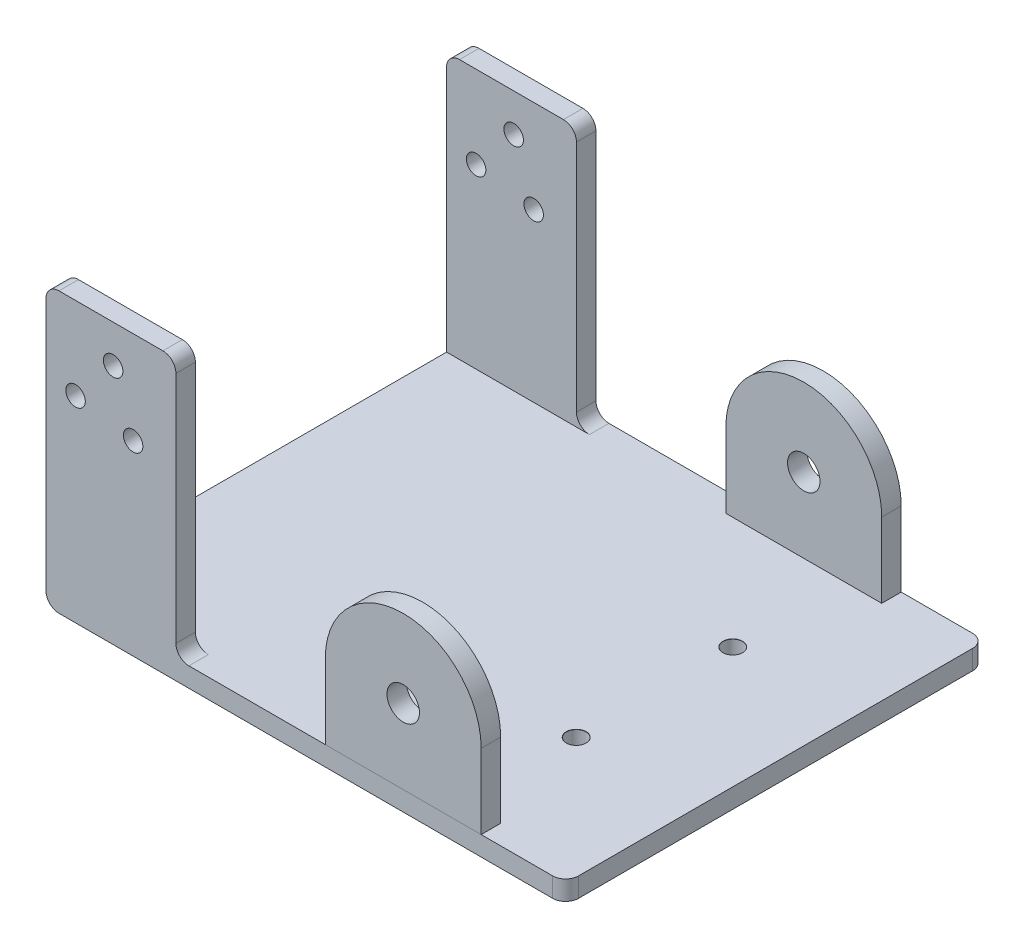
SolidWorks part; units mm, degrees
material "ABS"
ref_plane "Front Plane" through (0, 0, 0) normal (0, 0, 1) x (1, 0, 0)
ref_plane "Top Plane" through (0, 0, 0) normal (0, 1, 0) x (1, 0, 0)
ref_plane "Right Plane" through (0, 0, 0) normal (1, 0, 0) x (0, 0, -1)
sketch "Sketch1" plane through (0, 0, 0) normal (0, 1, 0) x (1, 0, 0)
  line L1 (-40, -32.335) -> (40, -32.335)
  line L2 (-40, -32.335) -> (-40, 32.335)
  line L3 (-40, 32.335) -> (40, 32.335)
  line L4 (40, -32.335) -> (40, 32.335)
  line L5 (-40, -32.335) -> (40, 32.335) construction
  line L6 (-40, 32.335) -> (40, -32.335) construction
  point P0 (0, 0)
  dimension "D1" = 80
  dimension "D2" = 64.67
extrude "Boss-Extrude1" add sketch "Sketch1" along normal blind 3
sketch "Sketch2" plane through (0, 3, 0) normal (0, 1, 0) x (1, 0, 0)
  line L1 (-40, 32.335) -> (-20, 32.335)
  line L2 (-40, 32.335) -> (-40, 29.335)
  line L3 (-40, 29.335) -> (-20, 29.335)
  line L4 (-20, 32.335) -> (-20, 29.335)
  line L5 (-40, -32.335) -> (-20, -32.335)
  line L6 (-40, -32.335) -> (-40, -29.335)
  line L7 (-40, -29.335) -> (-20, -29.335)
  line L8 (-20, -32.335) -> (-20, -29.335)
  dimension "D1" = 3
  dimension "D2" = 20
extrude "Boss-Extrude2" add sketch "Sketch2" along normal blind 40
hole_wizard "Ø3.0mm Dowel Hole1" positions "Sketch3" profile "Sketch4" hole size "Ø3.0" standard "ANSI Metric" end condition through all
sketch "Sketch3" plane through (0, 0, -32.335) normal (0, 0, -1) x (-1, 0, 0)
  point P0 (26.5872, 28.721)
  point P3 (35.4504, 30.2838)
  point P6 (29.6653, 37.1782)
sketch "Sketch4" plane through (-26.5872, 28.721, -32.335) normal (1, 0, 0) x (0, 1, 0)
  line L0 (0, 0) -> (0, 64.67)
  line L1 (0, 64.67) -> (1.5, 64.67)
  line L2 (1.5, 64.67) -> (1.5, 0.025)
  line L3 (1.5, 0.025) -> (1.525, 0)
  line L5 (1.525, 0) -> (0, 0)
  line L6 (-1.5, 0.025) -> (-1.525, 0) construction
  line L11 (0, -6.35) -> (0, 107.95) construction
  dimension "Thru Hole Dia." = 3
  dimension "Thru Hole Depth" = 64.67
  dimension "Near C'Sink Dia." = 3.05
  dimension "Near C'Sink Angle" = 90
fillet "Fillet1" radius 2 9 edges at (40, 1.5, -32.335) (40, 1.5, 32.335) (-40, 43, -30.835) (-20, 3, -30.835) (-20, 3, 30.835) (-20, 43, 30.835) (-40, 43, 30.835) (-20, 43, -30.835) (-40, 0, 0)
hole_wizard "Ø3.0mm Dowel Hole2" positions "Sketch7" profile "Sketch8" hole size "Ø3.0" standard "ANSI Metric" end condition through all
sketch "Sketch7" plane through (0, 3, 0) normal (0, 1, 0) x (1, 0, 0)
  point P0 (21.35, 12.05)
  point P3 (21.35, -12.05)
sketch "Sketch8" plane through (21.35, 3, -12.05) normal (1, 0, 0) x (0, 0, 1)
  line L0 (0, 0) -> (0, 3)
  line L1 (0, 3) -> (1.5, 3)
  line L2 (1.5, 3) -> (1.5, 0.025)
  line L3 (1.5, 0.025) -> (1.525, 0)
  line L5 (1.525, 0) -> (0, 0)
  line L6 (-1.5, 0.025) -> (-1.525, 0) construction
  line L11 (0, -6.35) -> (0, 107.95) construction
  dimension "Thru Hole Dia." = 3
  dimension "Thru Hole Depth" = 3
  dimension "Near C'Sink Dia." = 3.05
  dimension "Near C'Sink Angle" = 90
sketch "Sketch9" plane through (0, 0, -32.335) normal (0, 0, -1) x (-1, 0, 0)
  line L0 (-27, 3) -> (-27, 14.5)
  line L1 (-38, 3) -> (18, 3) construction
  line L2 (-27, 3) -> (-3, 3)
  line L3 (-3, 3) -> (-3, 14.5)
  line L4 (-40, 0) -> (-40, 3) construction
  line L5 (-38, 0) -> (38, 0) construction
  arc A0 (-27, 14.5) -> (-3, 14.5) centre (-15, 14.5) cw
  circle A1 centre (-15, 14.5) radius 2.5
  dimension "D3" = 12
  dimension "D4" = 5
  dimension "D1" = 25
  dimension "D2" = 14.5
extrude "Boss-Extrude3" add sketch "Sketch9" against normal blind 3 separate body
sketch "Sketch10" plane through (0, 0, 32.335) normal (0, 0, 1) x (1, 0, 0)
  line L0 (-18, 3) -> (38, 3) construction
  line L1 (3, 3) -> (27, 3)
  line L3 (3, 3) -> (27, 3)
  line L4 (27, 3) -> (27, 14.5)
  line L5 (3, 14.5) -> (3, 3)
  line L7 (27, 3) -> (27, 14.5)
  line L8 (3, 14.5) -> (3, 3)
  circle A0 centre (15, 14.5) radius 2.5 construction
  arc A1 (27, 14.5) -> (3, 14.5) centre (15, 14.5) ccw
  arc A2 (27, 14.5) -> (3, 14.5) centre (15, 14.5) ccw
  circle A3 centre (15, 14.5) radius 2.5
  dimension "D1" = 0
extrude "Boss-Extrude4" add sketch "Sketch10" against normal blind 3 separate body
